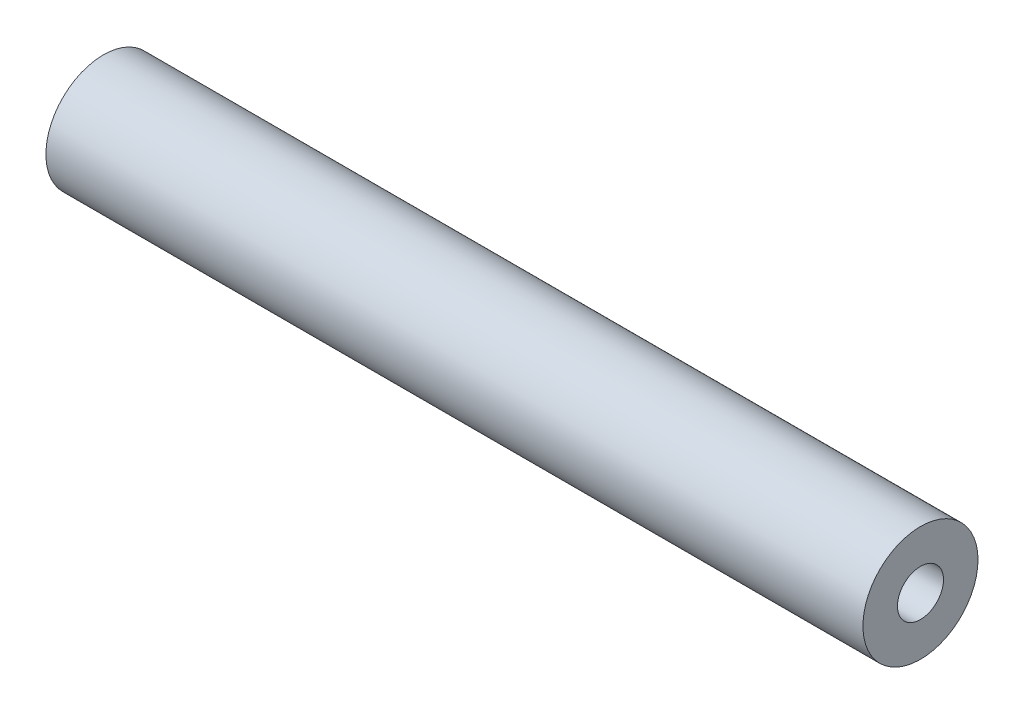
SolidWorks part; units mm, degrees
material "Pool Noodle"
ref_plane "Front" through (0, 0, 0) normal (0, 0, 1) x (1, 0, 0)
ref_plane "Top" through (0, 0, 0) normal (0, 1, 0) x (1, 0, 0)
ref_plane "Right" through (0, 0, 0) normal (1, 0, 0) x (0, 0, -1)
sketch "Sketch1" plane through (0, 0, 0) normal (1, 0, 0) x (0, 0, -1)
  circle A0 centre (0, 0) radius 12.7
  circle A1 centre (0, 0) radius 31.75
  dimension "D1" = 25.4
  dimension "D2" = 63.5
extrude "Boss-Extrude1" add sketch "Sketch1" along normal mid plane 450.85
